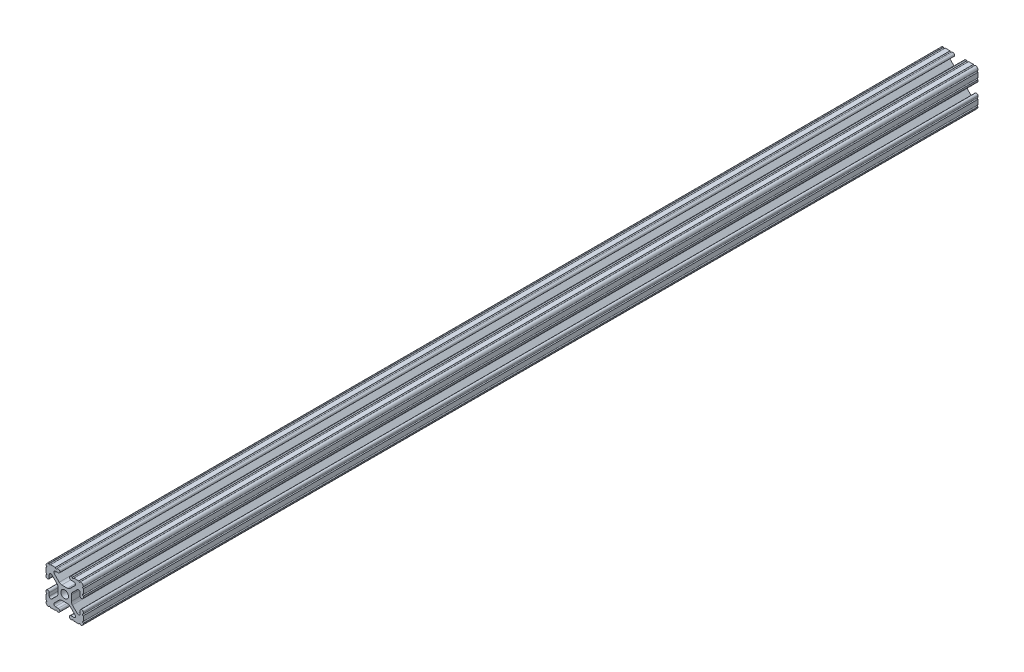
SolidWorks part; units mm, degrees
ref_plane "Front Plane" through (0, 0, 0) normal (0, 0, 1) x (1, 0, 0)
ref_plane "Top Plane" through (0, 0, 0) normal (0, 1, 0) x (1, 0, 0)
ref_plane "Right Plane" through (0, 0, 0) normal (1, 0, 0) x (0, 0, -1)
sketch "Sketch1" plane through (0, 0, 0) normal (0, 0, 1) x (1, 0, 0)
  line L0 (0, -12.7) -> (0, 12.7) construction
  line L1 (12.7, 0) -> (-12.7, 0) construction
  line L2 (3.2512, 12.7) -> (-3.2512, 12.7) construction
  line L3 (0, -4.5212) -> (0, 4.5212) construction
  line L4 (-3.2512, 12.7) -> (-3.2512, 10.4902) construction
  line L5 (12.7, -7.4168) -> (12.7, 7.4168) construction
  line L6 (0, -2.6035) -> (0, 2.6035) construction
  point P4 (0, 0)
  point P8 (0, 0)
  point P11 (0, 12.7)
  point P14 (0, 0)
  point P18 (12.7, 0)
  point P21 (0, 0)
sketch "Sketch2" plane through (0, 0, 0) normal (1, 0, 0) x (0, 0, -1)
  line L0 (-304.8, 0) -> (304.8, 0) construction
  point P4 (0, 0)
  dimension "Length" = 609.6
sketch "Sketch3" plane through (0, 0, 0) normal (0, 0, 1) x (1, 0, 0)
  line L1 (12.7, -12.7) -> (-12.7, -12.7)
  line L2 (12.7, -12.7) -> (12.7, 12.7)
  line L3 (12.7, 12.7) -> (-12.7, 12.7)
  line L4 (-12.7, -12.7) -> (-12.7, 12.7)
  line L5 (12.7, -12.7) -> (-12.7, 12.7) construction
  line L6 (12.7, 12.7) -> (-12.7, -12.7) construction
  point P0 (0, 0)
extrude "Boss-Extrude1" add sketch "Sketch3" along normal up to vertex (304.8 mm away) and the other way up to vertex (304.8 mm away) up to point (0, 0, 304.8) other way up to point (0, 0, -304.8)
sketch "Sketch4" plane through (0, 0, 304.8) normal (0, 0, 1) x (1, 0, 0)
  line L0 (-3.2512, 12.7) -> (-3.2512, 10.4902)
  line L1 (-3.2512, 10.4902) -> (-8.9276, 10.4902)
  line L2 (-8.9276, 10.4902) -> (-2.9586, 4.5212)
  line L3 (-2.9586, 4.5212) -> (2.9586, 4.5212)
  line L4 (0, -12.7) -> (0, 12.7) construction
  line L5 (12.7, 12.7) -> (-12.7, 12.7) construction
  line L6 (0, 12.7) -> (0, -12.7) construction
  line L7 (-12.7, 0) -> (12.7, 0) construction
  line L8 (-12.7, 12.7) -> (0, 0) construction
  line L9 (-12.7, 3.2512) -> (-10.4902, 3.2512)
  line L10 (-10.4902, 3.2512) -> (-10.4902, 8.9276)
  line L11 (-10.4902, 8.9276) -> (-4.5212, 2.9586)
  line L12 (-4.5212, 2.9586) -> (-4.5212, -2.9586)
  line L13 (4.5212, 2.9586) -> (4.5212, -2.9586)
  line L14 (10.4902, 8.9276) -> (4.5212, 2.9586)
  line L15 (10.4902, 3.2512) -> (10.4902, 8.9276)
  line L16 (12.7, 3.2512) -> (10.4902, 3.2512)
  line L17 (8.9276, 10.4902) -> (2.9586, 4.5212)
  line L18 (3.2512, 10.4902) -> (8.9276, 10.4902)
  line L19 (3.2512, 12.7) -> (3.2512, 10.4902)
  line L20 (3.2512, -12.7) -> (3.2512, -10.4902)
  line L21 (3.2512, -10.4902) -> (8.9276, -10.4902)
  line L22 (8.9276, -10.4902) -> (2.9586, -4.5212)
  line L23 (12.7, -3.2512) -> (10.4902, -3.2512)
  line L24 (10.4902, -3.2512) -> (10.4902, -8.9276)
  line L25 (10.4902, -8.9276) -> (4.5212, -2.9586)
  line L26 (-10.4902, -8.9276) -> (-4.5212, -2.9586)
  line L27 (-10.4902, -3.2512) -> (-10.4902, -8.9276)
  line L28 (-12.7, -3.2512) -> (-10.4902, -3.2512)
  line L29 (-2.9586, -4.5212) -> (2.9586, -4.5212)
  line L30 (-8.9276, -10.4902) -> (-2.9586, -4.5212)
  line L31 (-3.2512, -10.4902) -> (-8.9276, -10.4902)
  line L32 (-3.2512, -12.7) -> (-3.2512, -10.4902)
  line L33 (-12.7, 3.2512) -> (-12.7, -3.2512)
  line L34 (-3.2512, -12.7) -> (3.2512, -12.7)
  line L35 (12.7, -3.2512) -> (12.7, 3.2512)
  line L36 (3.2512, 12.7) -> (-3.2512, 12.7)
  line L37 (-12.7, 12.7) -> (-12.7, -12.7) construction
  line L38 (-12.7, -12.7) -> (12.7, -12.7) construction
  arc A3 (-6.3485, 10.4902) -> (-7.1039, 8.6665) centre (-6.3485, 9.4219) ccw
  arc A4 (7.1039, 8.6665) -> (6.3485, 10.4902) centre (6.3485, 9.4219) ccw
  arc A5 (8.6665, -7.1039) -> (10.4902, -6.3485) centre (9.4219, -6.3485) ccw
  arc A6 (10.4902, 6.3485) -> (8.6665, 7.1039) centre (9.4219, 6.3485) ccw
  arc A7 (-7.1039, -8.6665) -> (-6.3485, -10.4902) centre (-6.3485, -9.4219) ccw
  arc A8 (6.3485, -10.4902) -> (7.1039, -8.6665) centre (6.3485, -9.4219) ccw
  arc A9 (-8.6665, 7.1039) -> (-10.4902, 6.3485) centre (-9.4219, 6.3485) ccw
  arc A10 (-10.4902, -6.3485) -> (-8.6665, -7.1039) centre (-9.4219, -6.3485) ccw
  circle A11 centre (0, 0) radius 2.6035
  point P34 (0, 4.5212)
  point P45 (4.5212, 0)
  point P46 (-4.5212, 0)
  point P53 (0, -4.5212)
  point P81 (0, 0)
  line M2 (-12.7, 12.7) -> (-12.7, -12.7)
  line M3 (-12.7, -12.7) -> (12.7, -12.7)
  line M4 (12.7, -12.7) -> (12.7, 12.7)
  line M5 (12.7, 12.7) -> (-12.7, 12.7)
  dimension "D5" = 5.207
  dimension "D1" = 2.2098
  dimension "D2" = 2.2098
  dimension "D3" = 14.8336
  dimension "D4" = 4
extrude "Cut-Extrude1" cut sketch "Sketch4" against normal through all contours L17 A4 L18 L19 L0 L1 A3 L2 L3 M5 | L15 A6 L14 L13 L25 A5 L24 L23 L16 M4 | L21 A8 L22 L29 L30 A7 L31 L32 L20 M3 | L27 A10 L26 L12 L11 A9 L10 L9 L28 M2 | A11
sketch "Sketch5" plane through (0, 0, 304.8) normal (0, 0, 1) x (1, 0, 0)
  line L0 (-4.3561, 12.7) -> (-3.2512, 12.7)
  line L1 (-3.2512, 12.7) -> (-3.2512, 10.4902)
  line L2 (-3.2512, 10.4902) -> (-4.3561, 10.4902)
  line L3 (0, -12.7) -> (0, 12.7) construction
  line L4 (-3.2512, 12.7) -> (-12.7, 12.7) construction
  line L5 (3.2512, 10.4902) -> (4.3561, 10.4902)
  line L6 (3.2512, 12.7) -> (3.2512, 10.4902)
  line L7 (4.3561, 12.7) -> (3.2512, 12.7)
  line L8 (12.7, 4.3561) -> (12.7, 3.2512)
  line L9 (12.7, 3.2512) -> (10.4902, 3.2512)
  line L10 (10.4902, 3.2512) -> (10.4902, 4.3561)
  line L11 (10.4902, -3.2512) -> (10.4902, -4.3561)
  line L12 (12.7, -3.2512) -> (10.4902, -3.2512)
  line L13 (12.7, -4.3561) -> (12.7, -3.2512)
  line L14 (4.3561, -12.7) -> (3.2512, -12.7)
  line L15 (3.2512, -12.7) -> (3.2512, -10.4902)
  line L16 (3.2512, -10.4902) -> (4.3561, -10.4902)
  line L17 (-3.2512, -10.4902) -> (-4.3561, -10.4902)
  line L18 (-3.2512, -12.7) -> (-3.2512, -10.4902)
  line L19 (-4.3561, -12.7) -> (-3.2512, -12.7)
  line L20 (-12.7, -4.3561) -> (-12.7, -3.2512)
  line L21 (-12.7, -3.2512) -> (-10.4902, -3.2512)
  line L22 (-10.4902, -3.2512) -> (-10.4902, -4.3561)
  line L23 (-10.4902, 3.2512) -> (-10.4902, 4.3561)
  line L24 (-12.7, 3.2512) -> (-10.4902, 3.2512)
  line L25 (-12.7, 4.3561) -> (-12.7, 3.2512)
  line L26 (-12.7, 12.7) -> (-12.7, 3.2512) construction
  line L27 (-10.7124, 12.7) -> (-9.6075, 12.7)
  line L28 (-6.3436, 12.7) -> (-5.2387, 12.7)
  line L29 (-12.7, 10.7124) -> (-12.7, 9.6075)
  line L30 (-12.7, 6.3436) -> (-12.7, 5.2387)
  line L31 (6.3437, 12.7) -> (5.2388, 12.7)
  line L32 (10.7125, 12.7) -> (9.6076, 12.7)
  line L33 (12.7, 10.7125) -> (12.7, 9.6075)
  line L34 (12.7, 6.3436) -> (12.7, 5.2387)
  line L35 (12.7, -6.3437) -> (12.7, -5.2388)
  line L36 (12.7, -10.7125) -> (12.7, -9.6076)
  line L37 (10.7125, -12.7) -> (9.6076, -12.7)
  line L38 (6.3437, -12.7) -> (5.2388, -12.7)
  line L39 (-6.3436, -12.7) -> (-5.2387, -12.7)
  line L40 (-10.7124, -12.7) -> (-9.6075, -12.7)
  line L41 (-12.7, -10.7125) -> (-12.7, -9.6076)
  line L42 (-12.7, -6.3437) -> (-12.7, -5.2388)
  line L43 (12.7, 12.7) -> (3.2512, 12.7) construction
  line L44 (12.7, 3.2512) -> (12.7, 12.7) construction
  arc A0 (-4.3561, 10.4902) -> (-4.3561, 12.7) centre (-4.3561, 11.5951) ccw
  arc A1 (4.3561, 10.4902) -> (4.3561, 12.7) centre (4.3561, 11.5951) cw
  arc A2 (10.4902, 4.3561) -> (12.7, 4.3561) centre (11.5951, 4.3561) ccw
  arc A3 (10.4902, -4.3561) -> (12.7, -4.3561) centre (11.5951, -4.3561) cw
  arc A4 (4.3561, -10.4902) -> (4.3561, -12.7) centre (4.3561, -11.5951) ccw
  arc A5 (-4.3561, -10.4902) -> (-4.3561, -12.7) centre (-4.3561, -11.5951) cw
  arc A6 (-10.4902, -4.3561) -> (-12.7, -4.3561) centre (-11.5951, -4.3561) ccw
  arc A7 (-10.4902, 4.3561) -> (-12.7, 4.3561) centre (-11.5951, 4.3561) cw
  arc A8 (-10.7124, 12.7) -> (-9.6075, 12.7) centre (-10.16, 12.7) ccw
  arc A9 (-6.3436, 12.7) -> (-5.2387, 12.7) centre (-5.7912, 12.7) ccw
  arc A10 (-12.7, 9.6075) -> (-12.7, 10.7124) centre (-12.7, 10.16) ccw
  arc A11 (-12.7, 5.2387) -> (-12.7, 6.3436) centre (-12.7, 5.7912) ccw
  arc A12 (5.2388, 12.7) -> (6.3437, 12.7) centre (5.7912, 12.7) ccw
  arc A13 (9.6076, 12.7) -> (10.7125, 12.7) centre (10.16, 12.7) ccw
  arc A14 (12.7, 10.7125) -> (12.7, 9.6075) centre (12.7, 10.16) ccw
  arc A15 (12.7, 6.3436) -> (12.7, 5.2387) centre (12.7, 5.7912) ccw
  arc A16 (12.7, -5.2388) -> (12.7, -6.3437) centre (12.7, -5.7912) ccw
  arc A17 (12.7, -9.6076) -> (12.7, -10.7125) centre (12.7, -10.16) ccw
  arc A18 (10.7125, -12.7) -> (9.6076, -12.7) centre (10.16, -12.7) ccw
  arc A19 (6.3437, -12.7) -> (5.2388, -12.7) centre (5.7912, -12.7) ccw
  arc A20 (-5.2387, -12.7) -> (-6.3436, -12.7) centre (-5.7912, -12.7) ccw
  arc A21 (-9.6075, -12.7) -> (-10.7124, -12.7) centre (-10.16, -12.7) ccw
  arc A22 (-12.7, -10.7125) -> (-12.7, -9.6076) centre (-12.7, -10.16) ccw
  arc A23 (-12.7, -6.3437) -> (-12.7, -5.2388) centre (-12.7, -5.7912) ccw
  point P11 (0, 0)
  point P52 (0, 0)
  point P104 (0, 0)
  line M5 (3.2512, -10.4902) -> (3.2512, -12.7)
  line M6 (3.2512, -12.7) -> (12.7, -12.7)
  line M7 (12.7, -12.7) -> (12.7, -3.2512)
  line M8 (12.7, -3.2512) -> (10.4902, -3.2512)
  line M9 (10.4902, -3.2512) -> (10.4902, -6.3485)
  line M15 (10.4902, 6.3485) -> (10.4902, 3.2512)
  line M16 (10.4902, 3.2512) -> (12.7, 3.2512)
  line M17 (12.7, 3.2512) -> (12.7, 12.7)
  line M18 (12.7, 12.7) -> (3.2512, 12.7)
  line M19 (3.2512, 12.7) -> (3.2512, 10.4902)
  line M20 (3.2512, 10.4902) -> (6.3485, 10.4902)
  line M26 (-6.3485, 10.4902) -> (-3.2512, 10.4902)
  line M27 (-3.2512, 10.4902) -> (-3.2512, 12.7)
  line M28 (-3.2512, 12.7) -> (-12.7, 12.7)
  line M29 (-12.7, 12.7) -> (-12.7, 3.2512)
  line M30 (-12.7, 3.2512) -> (-10.4902, 3.2512)
  line M31 (-10.4902, 3.2512) -> (-10.4902, 6.3485)
  line M37 (-10.4902, -6.3485) -> (-10.4902, -3.2512)
  line M38 (-10.4902, -3.2512) -> (-12.7, -3.2512)
  line M39 (-12.7, -3.2512) -> (-12.7, -12.7)
  line M40 (-12.7, -12.7) -> (-3.2512, -12.7)
  line M41 (-3.2512, -12.7) -> (-3.2512, -10.4902)
  line M42 (-3.2512, -10.4902) -> (-6.3485, -10.4902)
  line M48 (6.3485, -10.4902) -> (3.2512, -10.4902)
  dimension "D2" = 0.5524
  dimension "D3" = 2.54
  dimension "D4" = 2.54
  dimension "D5" = 2.54
  dimension "D6" = 2.54
  dimension "D1" = 4
  dimension "D7" = 4
extrude "Cut-Extrude2" cut sketch "Sketch5" against normal through all contours A7 M30 M29 | A7 L24 M31 | A6 L21 M39 | A6 M37 M38 | A5 L18 M42 | A5 M41 M40 | A4 M48 M5 | A4 L15 M6 | A3 L12 M9 | A3 M8 M7 | A2 M15 M16 | A2 L9 M17 | A1 M19 M18 | A1 L6 M20 | A0 L1 M28 | A0 M26 M27 | A11 L30 | A10 L29 | A8 L27 | A9 L28 | L31 A12 | L32 A13 | L33 A14 | L34 A15 | L42 A23 | L41 A22 | L40 A21 | L39 A20 | L36 A17 | L35 A16 | L37 A18 | L38 A19
fillet "Fillet1" radius 2.54 8 edges at (2.9586, -4.5212, 0) (-2.9586, -4.5212, 0) (4.5212, -2.9586, 0) (4.5212, 2.9586, 0) (-2.9586, 4.5212, 0) (2.9586, 4.5212, 0) (-4.5212, -2.9586, 0) (-4.5212, 2.9586, 0)
fillet "Fillet2" radius 1.778 4 edges at (12.7, -12.7, 0) (12.7, 12.7, 0) (-12.7, -12.7, 0) (-12.7, 12.7, 0)
equation "\"D2@Sketch4\"=\"Thickness@Sketch1\""
equation "\"D1@Sketch4\"=\"Thickness@Sketch1\""
equation "\"D3@Sketch4\"=\"Opening Width@Sketch1\""
equation "\"D5@Sketch4\"=\"Hole Dia@Sketch1\""
equation "\"D2@Sketch5\"=\"Thickness@Sketch1\"/4"
equation "\"D3@Sketch5\"=\"Height@Sketch1\"/10"
equation "\"D4@Sketch5\"=\"D3@Sketch5\""
equation "\"D5@Sketch5\"=\"D4@Sketch5\""
equation "\"D6@Sketch5\"=\"D5@Sketch5\""
